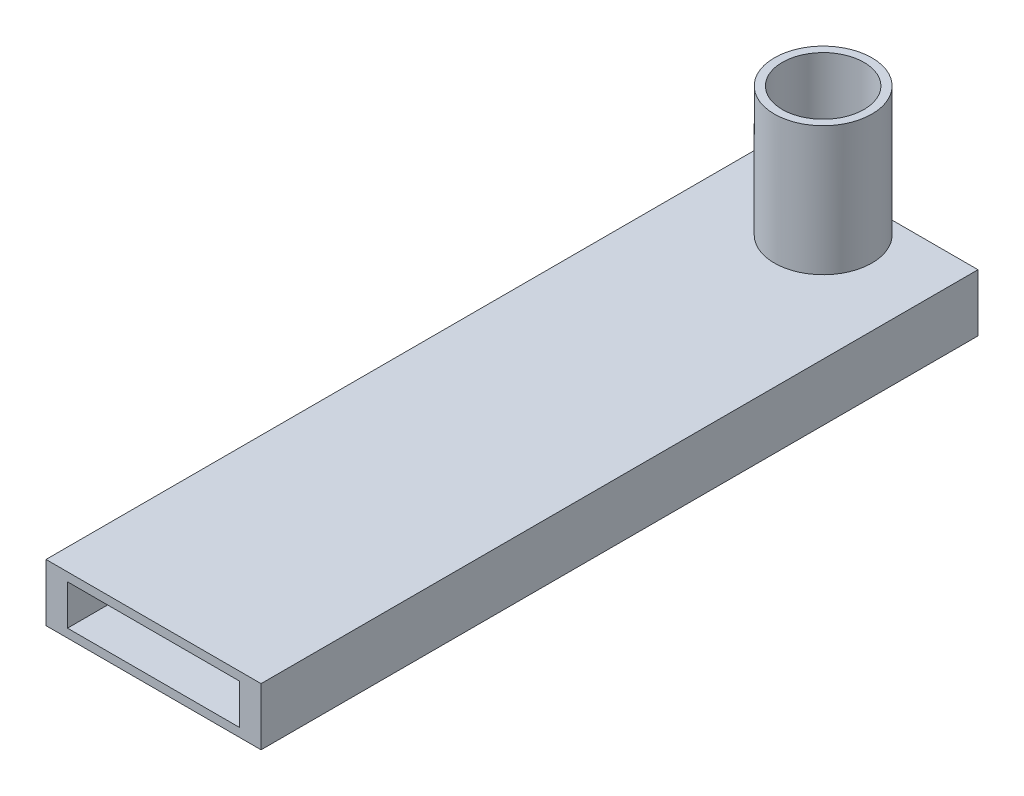
SolidWorks part; units mm, degrees
ref_plane "Front Plane" through (0, 0, 0) normal (0, 0, 1) x (1, 0, 0)
ref_plane "Top Plane" through (0, 0, 0) normal (0, 1, 0) x (1, 0, 0)
ref_plane "Right Plane" through (0, 0, 0) normal (1, 0, 0) x (0, 0, -1)
sketch "Sketch1" plane through (0, 0, 0) normal (0, 0, 1) x (1, 0, 0)
  line L1 (-19.05, -5.08) -> (19.05, -5.08)
  line L2 (-19.05, -5.08) -> (-19.05, 5.08)
  line L3 (-19.05, 5.08) -> (19.05, 5.08)
  line L4 (19.05, -5.08) -> (19.05, 5.08)
  line L5 (-19.05, -5.08) -> (19.05, 5.08) construction
  line L6 (-19.05, 5.08) -> (19.05, -5.08) construction
  point P0 (0, 0)
  dimension "D1" = 38.1
  dimension "D2" = 10.16
extrude "Boss-Extrude1" add sketch "Sketch1" against normal blind 127
sketch "Sketch2" plane through (0, 0, 0) normal (0, 0, 1) x (1, 0, 0)
  line L1 (-15.24, -3.556) -> (15.24, -3.556)
  line L2 (-15.24, -3.556) -> (-15.24, 3.556)
  line L3 (-15.24, 3.556) -> (15.24, 3.556)
  line L4 (15.24, -3.556) -> (15.24, 3.556)
  line L5 (-15.24, -3.556) -> (15.24, 3.556) construction
  line L6 (-15.24, 3.556) -> (15.24, -3.556) construction
  point P0 (0, 0)
  dimension "D1" = 30.48
  dimension "D2" = 7.112
extrude "Cut-Extrude1" cut sketch "Sketch2" against normal blind 25.4
sketch "Sketch3" plane through (0, 5.08, 0) normal (0, 1, 0) x (1, 0, 0)
  line L0 (-19.05, 127) -> (-19.05, 0) construction
  line L3 (19.05, 127) -> (-19.05, 127) construction
  circle A0 centre (0, 118.618) radius 7.239
  dimension "D3" = 14.478
  dimension "D1" = 19.05
  dimension "D2" = 8.382
extrude "Cut-Extrude2" cut sketch "Sketch3" against normal blind 6.35
sketch "Sketch4" plane through (0, -5.08, 0) normal (0, -1, 0) x (1, 0, 0)
  circle A0 centre (0, -118.618) radius 5.207
  circle A1 centre (0, -118.618) radius 7.239 construction
  dimension "D1" = 10.414
extrude "Cut-Extrude3" cut sketch "Sketch4" against normal through all
sketch "Sketch5" plane through (0, 5.08, 0) normal (0, 1, 0) x (1, 0, 0)
  circle A0 centre (0, 118.618) radius 8.6413
extrude "Boss-Extrude2" add sketch "Sketch5" along normal blind 22.86
sketch "Sketch6" plane through (0, 27.94, 0) normal (0, 1, 0) x (1, 0, 0)
  circle A0 centre (0, 118.618) radius 7.239
  point P0 (0, 118.618)
  dimension "D1" = 14.478
extrude "Cut-Extrude5" cut sketch "Sketch6" against normal blind 22.86 contours A0
